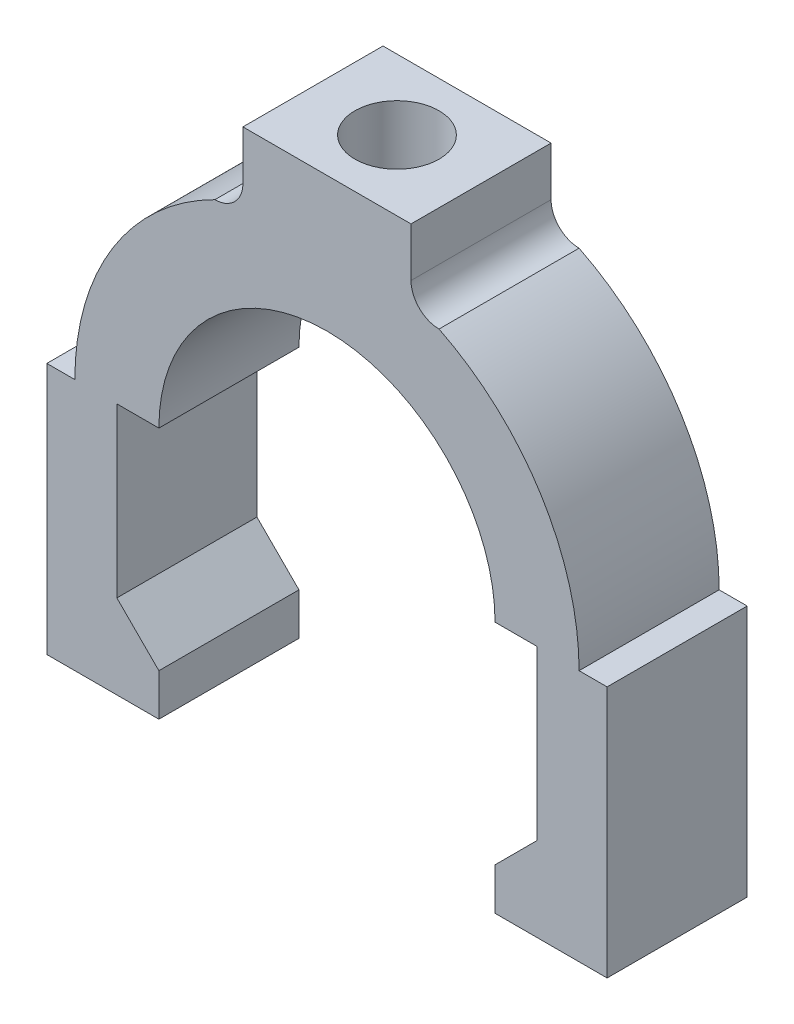
SolidWorks part; units mm, degrees
ref_plane "Front Plane" through (0, 0, 0) normal (0, 0, 1) x (1, 0, 0)
ref_plane "Top Plane" through (0, 0, 0) normal (0, 1, 0) x (1, 0, 0)
ref_plane "Right Plane" through (0, 0, 0) normal (1, 0, 0) x (0, 0, -1)
sketch "Sketch1" plane through (0, 0, 0) normal (0, 0, 1) x (1, 0, 0)
  line L2 (0, 0) -> (0, -7)
  line L3 (0, 0) -> (24, 0)
  line L4 (-28, -43.249) -> (-24, -43.249)
  line L5 (-28, -43.249) -> (-28, -79.249)
  line L6 (-28, -79.249) -> (-12, -79.249)
  line L7 (-12, -79.249) -> (-12, -73.249)
  line L8 (-24, -43.249) -> (-28, -43.249)
  line L9 (-18, -43.249) -> (-12, -43.249)
  line L10 (-18, -43.249) -> (-18, -67.249)
  line L11 (-12, -73.249) -> (-18, -67.249)
  line L12 (52, -79.249) -> (36, -79.249)
  line L13 (36, -79.249) -> (36, -73.249)
  line L14 (36, -73.249) -> (42, -67.249)
  line L15 (42, -43.249) -> (36, -43.249)
  line L16 (42, -43.249) -> (42, -67.249)
  line L17 (52, -43.249) -> (48, -43.249)
  line L18 (52, -43.249) -> (52, -79.249)
  line L19 (24, 0) -> (24, -7)
  arc A0 (-4, -11) -> (0, -7) centre (-4, -7) ccw
  arc A1 (-4, -11) -> (-24, -43.249) centre (12, -43.249) ccw
  arc A2 (36, -43.249) -> (-12, -43.249) centre (12, -43.249) ccw
  arc A3 (28, -11) -> (24, -7) centre (28, -7) cw
  arc A4 (28, -11) -> (48, -43.249) centre (12, -43.249) cw
  dimension "D2" = 6
  dimension "D3" = 6
  dimension "D4" = 135
extrude "Boss-Extrude1" add sketch "Sketch1" along normal blind 20 contours L19 A3 A4 L17 L18 L12 L13 L14 L16 L15 A2 L9 L10 L11 L7 L6 L5 L4 A1 A0 L2 L3
sketch "Sketch2" plane through (0, 0, 0) normal (0, 1, 0) x (1, 0, 0)
  circle A0 centre (12, -10) radius 6
extrude "Cut-Extrude1" cut sketch "Sketch2" against normal blind 20
